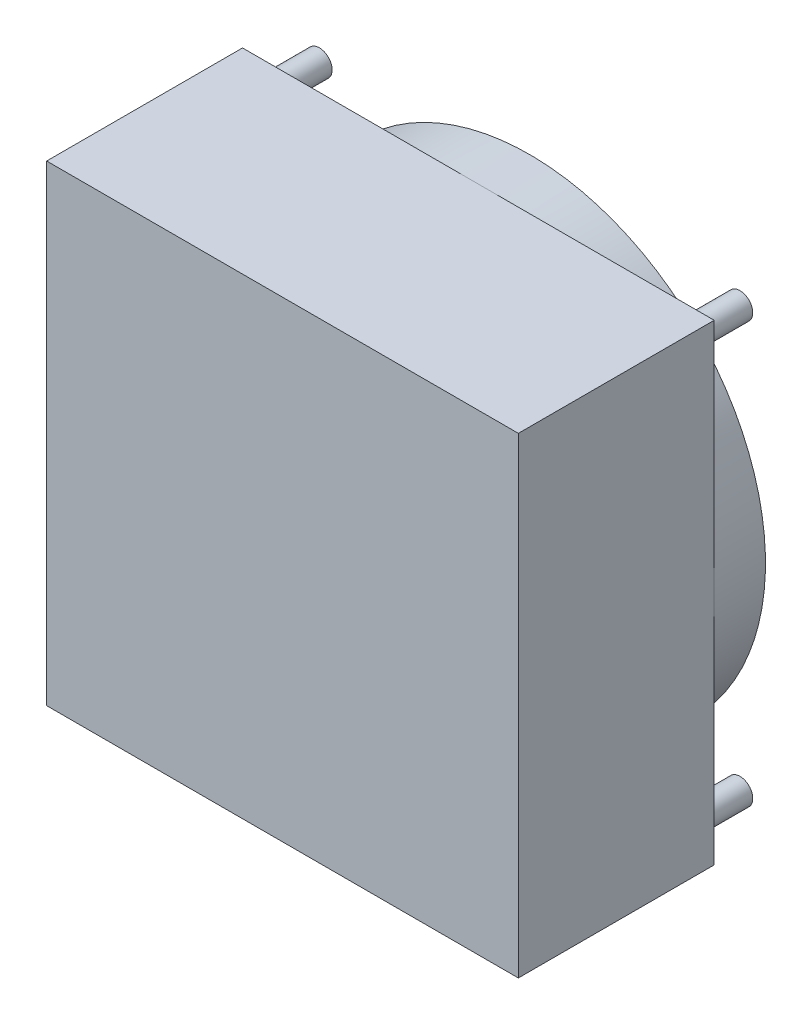
SolidWorks part; units mm, degrees
ref_plane "Front Plane" through (0, 0, 0) normal (0, 0, 1) x (1, 0, 0)
ref_plane "Top Plane" through (0, 0, 0) normal (0, 1, 0) x (1, 0, 0)
ref_plane "Right Plane" through (0, 0, 0) normal (1, 0, 0) x (0, 0, -1)
sketch "Sketch2" plane through (0, 0, 0) normal (0, 0, 1) x (1, 0, 0)
  line L1 (0, 0) -> (92, 0)
  line L2 (0, 0) -> (0, 92)
  line L3 (0, 92) -> (92, 92)
  line L4 (92, 0) -> (92, 92)
  dimension "D1" = 92
  dimension "D2" = 92
extrude "Boss-Extrude1" add sketch "Sketch2" along normal blind 38.2
sketch "Sketch3" plane through (0, 0, 0) normal (0, 0, -1) x (-1, 0, 0)
  line L0 (0, 4.98) -> (-92, 4.98) construction
  line L1 (0, 92) -> (0, 0) construction
  line L2 (-92, 0) -> (-92, 92) construction
  line L3 (0, 0) -> (-92, 0) construction
  line L4 (0, 46) -> (-92, 46) construction
  line L5 (-46, 92) -> (-46, 0) construction
  line L6 (-92, 92) -> (0, 92) construction
  circle A0 centre (-4.98, 4.98) radius 2.5
  circle A1 centre (-87.02, 4.98) radius 2.5
  circle A2 centre (-87.02, 87.02) radius 2.5
  circle A3 centre (-4.98, 87.02) radius 2.5
  point P16 (-46, 46)
  dimension "D1" = 5
  dimension "D2" = 4.98
  dimension "D3" = 4.98
  dimension "D4" = 4
extrude "Boss-Extrude2" add sketch "Sketch3" along normal blind 10
sketch "Sketch4" plane through (0, 0, 0) normal (0, 0, -1) x (-1, 0, 0)
  circle A0 centre (-46, 46) radius 46
  dimension "D1" = 92
extrude "Boss-Extrude3" add sketch "Sketch4" along normal blind 10
